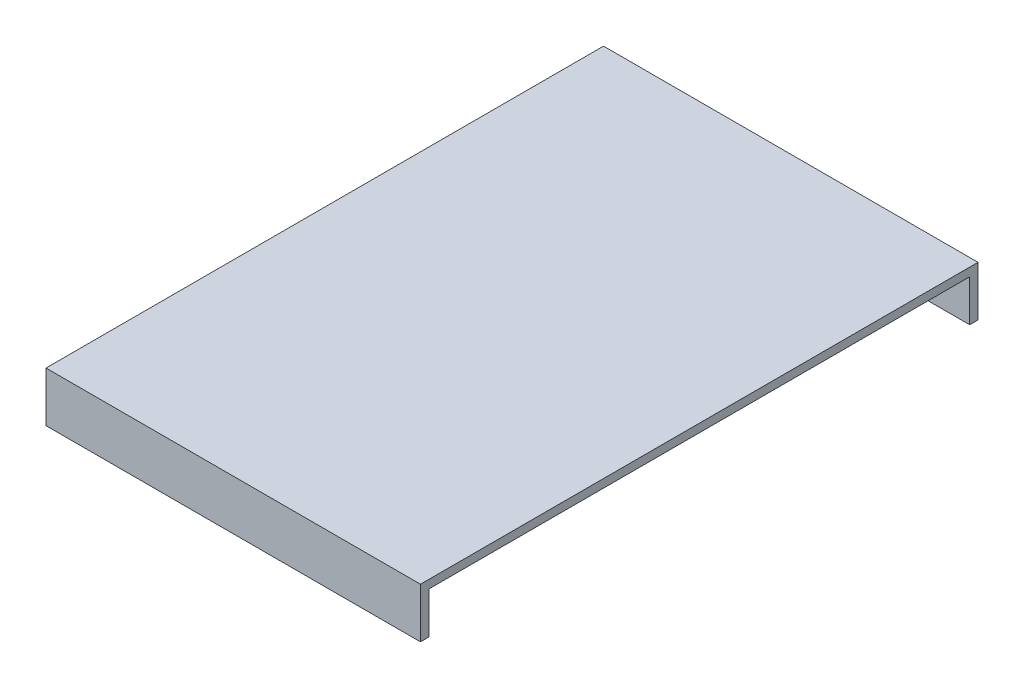
SolidWorks part; units mm, degrees
ref_plane "前视基准面" through (0, 0, 0) normal (0, 0, 1) x (1, 0, 0)
ref_plane "上视基准面" through (0, 0, 0) normal (0, 1, 0) x (1, 0, 0)
ref_plane "右视基准面" through (0, 0, 0) normal (1, 0, 0) x (0, 0, -1)
sketch "草图2" plane through (0, 0, 0) normal (0, 1, 0) x (1, 0, 0)
  line L1 (-0.5, 69.8511) -> (-45, 69.8511)
  line L2 (-45, 69.8511) -> (-45, -64.1489)
  line L3 (-45, -64.1489) -> (45, -64.1489)
  line L4 (45, -64.1489) -> (45, 69.8511)
  line L5 (45, 69.8511) -> (-0.5, 69.8511)
  dimension "D1" = 90
  dimension "D2" = 134
extrude "凸台-拉伸1" add sketch "草图2" along normal blind 2
sketch "草图3" plane through (0, 0, 0) normal (0, 1, 0) x (1, 0, 0)
  line L0 (45, 69.8511) -> (45, 67.8511)
  line L1 (-45, 67.8511) -> (45, 67.8511)
  line L2 (-45, -64.1489) -> (45, -64.1489)
  line L3 (45, -64.1489) -> (45, -62.1489)
  line L4 (45, 69.8511) -> (-45, 69.8511)
  line L5 (-45, 69.8511) -> (-45, -64.1489)
  line L6 (-45, -64.1489) -> (45, -64.1489)
  line L7 (45, -64.1489) -> (45, 69.8511)
  line L8 (45, 69.8511) -> (-45, 69.8511)
  line L9 (-45, 69.8511) -> (-45, 67.8511)
  line L10 (45, -64.1489) -> (45, 69.8511) construction
  line L11 (45, -62.1489) -> (-45, -62.1489)
  line L12 (-45, 69.8511) -> (-45, -64.1489) construction
  line L13 (-45, -62.1489) -> (-45, -64.1489)
  dimension "D2" = 2
  dimension "D1" = 0
extrude "凸台-拉伸2" add sketch "草图3" against normal blind 10
